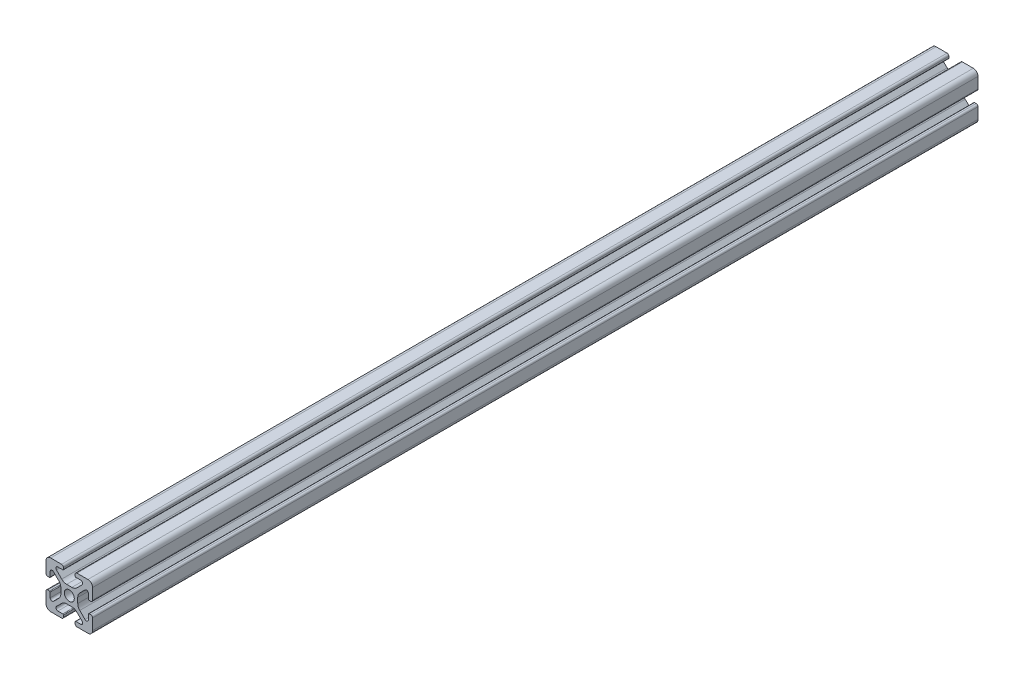
SolidWorks part; units mm, degrees
material "6061-T6 (SS)"
ref_plane "Front Plane" through (0, 0, 0) normal (0, 0, 1) x (1, 0, 0)
ref_plane "Top Plane" through (0, 0, 0) normal (0, 1, 0) x (1, 0, 0)
ref_plane "Right Plane" through (0, 0, 0) normal (1, 0, 0) x (0, 0, -1)
sketch "Sketch1" plane through (0, 0, 0) normal (0, 0, 1) x (1, 0, 0)
  line L2 (-9.9949, 7.9883) -> (-9.9949, 3.2893)
  line L3 (-7.9883, 9.9949) -> (-3.2893, 9.9949)
  line L4 (-2.5019, 9.2075) -> (-2.5019, 8.4963)
  line L5 (-2.8067, 8.1915) -> (-4.9149, 8.1915)
  line L6 (-5.5076, 6.7606) -> (-3.2528, 4.5058)
  line L7 (-6.7606, 5.5076) -> (-4.5058, 3.2528)
  line L8 (-8.1915, 4.9149) -> (-8.1915, 2.8067)
  line L9 (-8.4963, 2.5019) -> (-9.2075, 2.5019)
  line L11 (-1.1334, 3.6279) -> (1.1334, 3.6279)
  line L12 (-3.6279, 1.1334) -> (-3.6279, -1.1334)
  line L13 (8.4963, 2.5019) -> (9.2075, 2.5019)
  line L14 (8.1915, 4.9149) -> (8.1915, 2.8067)
  line L15 (9.9949, 7.9883) -> (9.9949, 3.2893)
  line L16 (7.9883, 9.9949) -> (3.2893, 9.9949)
  line L17 (2.5019, 9.2075) -> (2.5019, 8.4963)
  line L18 (2.8067, 8.1915) -> (4.9149, 8.1915)
  line L19 (3.6279, 1.1334) -> (3.6279, -1.1334)
  line L20 (5.5076, 6.7606) -> (3.2528, 4.5058)
  line L21 (6.7606, 5.5076) -> (4.5058, 3.2528)
  line L22 (-8.4963, -2.5019) -> (-9.2075, -2.5019)
  line L23 (-8.1915, -4.9149) -> (-8.1915, -2.8067)
  line L24 (-6.7606, -5.5076) -> (-4.5058, -3.2528)
  line L25 (-5.5076, -6.7606) -> (-3.2528, -4.5058)
  line L26 (-2.8067, -8.1915) -> (-4.9149, -8.1915)
  line L27 (-2.5019, -9.2075) -> (-2.5019, -8.4963)
  line L28 (-7.9883, -9.9949) -> (-3.2893, -9.9949)
  line L29 (-9.9949, -7.9883) -> (-9.9949, -3.2893)
  line L30 (9.9949, -7.9883) -> (9.9949, -3.2893)
  line L31 (7.9883, -9.9949) -> (3.2893, -9.9949)
  line L32 (2.5019, -9.2075) -> (2.5019, -8.4963)
  line L33 (2.8067, -8.1915) -> (4.9149, -8.1915)
  line L34 (5.5076, -6.7606) -> (3.2528, -4.5058)
  line L35 (6.7606, -5.5076) -> (4.5058, -3.2528)
  line L36 (8.1915, -4.9149) -> (8.1915, -2.8067)
  line L37 (8.4963, -2.5019) -> (9.2075, -2.5019)
  line L38 (-1.1334, -3.6279) -> (1.1334, -3.6279)
  circle A0 centre (0, 0) radius 2.1463
  arc A1 (-9.9949, 7.9883) -> (-7.9883, 9.9949) centre (-7.9883, 7.9883) cw
  arc A2 (-6.7606, 5.5076) -> (-8.1915, 4.9149) centre (-7.3533, 4.9149) ccw
  arc A3 (-4.9149, 8.1915) -> (-5.5076, 6.7606) centre (-4.9149, 7.3533) ccw
  arc A4 (-3.2893, 9.9949) -> (-2.5019, 9.2075) centre (-3.2893, 9.2075) cw
  arc A5 (-9.9949, 3.2893) -> (-9.2075, 2.5019) centre (-9.2075, 3.2893) ccw
  arc A6 (-8.1915, 2.8067) -> (-8.4963, 2.5019) centre (-8.4963, 2.8067) cw
  arc A7 (-2.5019, 8.4963) -> (-2.8067, 8.1915) centre (-2.8067, 8.4963) cw
  arc A8 (-1.1334, 3.6279) -> (-3.2528, 4.5058) centre (-1.1334, 6.6251) cw
  arc A9 (-3.6279, 1.1334) -> (-4.5058, 3.2528) centre (-6.6251, 1.1334) ccw
  arc A10 (8.1915, 2.8067) -> (8.4963, 2.5019) centre (8.4963, 2.8067) ccw
  arc A11 (9.9949, 3.2893) -> (9.2075, 2.5019) centre (9.2075, 3.2893) cw
  arc A12 (9.9949, 7.9883) -> (7.9883, 9.9949) centre (7.9883, 7.9883) ccw
  arc A13 (3.2893, 9.9949) -> (2.5019, 9.2075) centre (3.2893, 9.2075) ccw
  arc A14 (2.5019, 8.4963) -> (2.8067, 8.1915) centre (2.8067, 8.4963) ccw
  arc A15 (1.1334, 3.6279) -> (3.2528, 4.5058) centre (1.1334, 6.6251) ccw
  arc A16 (3.6279, 1.1334) -> (4.5058, 3.2528) centre (6.6251, 1.1334) cw
  arc A17 (6.7606, 5.5076) -> (8.1915, 4.9149) centre (7.3533, 4.9149) cw
  arc A18 (4.9149, 8.1915) -> (5.5076, 6.7606) centre (4.9149, 7.3533) cw
  arc A19 (-3.6279, -1.1334) -> (-4.5058, -3.2528) centre (-6.6251, -1.1334) cw
  arc A20 (-1.1334, -3.6279) -> (-3.2528, -4.5058) centre (-1.1334, -6.6251) ccw
  arc A21 (-2.5019, -8.4963) -> (-2.8067, -8.1915) centre (-2.8067, -8.4963) ccw
  arc A22 (-8.1915, -2.8067) -> (-8.4963, -2.5019) centre (-8.4963, -2.8067) ccw
  arc A23 (-9.9949, -3.2893) -> (-9.2075, -2.5019) centre (-9.2075, -3.2893) cw
  arc A24 (-3.2893, -9.9949) -> (-2.5019, -9.2075) centre (-3.2893, -9.2075) ccw
  arc A25 (-4.9149, -8.1915) -> (-5.5076, -6.7606) centre (-4.9149, -7.3533) cw
  arc A26 (-6.7606, -5.5076) -> (-8.1915, -4.9149) centre (-7.3533, -4.9149) cw
  arc A27 (-9.9949, -7.9883) -> (-7.9883, -9.9949) centre (-7.9883, -7.9883) ccw
  arc A28 (9.9949, -7.9883) -> (7.9883, -9.9949) centre (7.9883, -7.9883) cw
  arc A29 (6.7606, -5.5076) -> (8.1915, -4.9149) centre (7.3533, -4.9149) ccw
  arc A30 (4.9149, -8.1915) -> (5.5076, -6.7606) centre (4.9149, -7.3533) ccw
  arc A31 (3.2893, -9.9949) -> (2.5019, -9.2075) centre (3.2893, -9.2075) cw
  arc A32 (9.9949, -3.2893) -> (9.2075, -2.5019) centre (9.2075, -3.2893) ccw
  arc A33 (8.1915, -2.8067) -> (8.4963, -2.5019) centre (8.4963, -2.8067) cw
  arc A34 (2.5019, -8.4963) -> (2.8067, -8.1915) centre (2.8067, -8.4963) cw
  arc A35 (1.1334, -3.6279) -> (3.2528, -4.5058) centre (1.1334, -6.6251) cw
  arc A36 (3.6279, -1.1334) -> (4.5058, -3.2528) centre (6.6251, -1.1334) ccw
extrude "Boss-Extrude1" add sketch "Sketch1" along normal mid plane 380.0204
